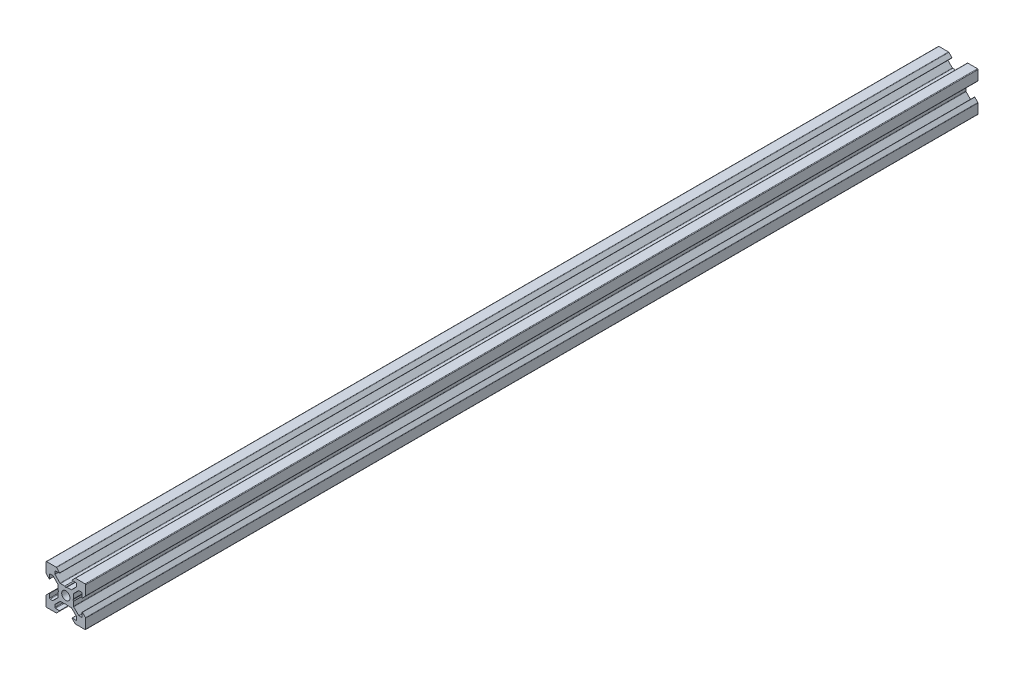
SolidWorks part; units mm, degrees
material "6063-T5"
ref_plane "Plan de face" through (0, 0, 0) normal (0, 0, 1) x (1, 0, 0)
ref_plane "Plan de dessus" through (0, 0, 0) normal (0, 1, 0) x (1, 0, 0)
ref_plane "Plan de droite" through (0, 0, 0) normal (1, 0, 0) x (0, 0, -1)
sketch "Esquisse1" plane through (0, 0, 0) normal (0, 0, 1) x (1, 0, 0)
  line L0 (18.7749, -2.8952) -> (18.7749, -4.8946)
  line L1 (18.4749, -5.1946) -> (17.2591, -5.1946)
  line L2 (17.047, -5.1067) -> (14.5634, -2.6231)
  line L3 (14.4755, -2.411) -> (14.4755, -0.2148)
  line L4 (14.4755, -0.2148) -> (14.1755, 0.3048)
  line L5 (14.1755, 0.3048) -> (14.4755, 0.8244)
  line L6 (14.4755, 0.8244) -> (14.4755, 3.0205)
  line L7 (14.5634, 3.2326) -> (17.047, 5.7162)
  line L8 (17.2591, 5.8041) -> (18.4749, 5.8041)
  line L9 (18.7749, 5.5041) -> (18.7749, 3.5048)
  line L10 (18.9456, 3.4341) -> (20.487, 4.9755)
  line L11 (20.5749, 5.1876) -> (20.5749, 10.0048)
  line L12 (20.2749, 10.3048) -> (15.4577, 10.3048)
  line L13 (15.2456, 10.2169) -> (13.7041, 8.6755)
  line L14 (13.7749, 8.5048) -> (15.7742, 8.5048)
  line L15 (16.0742, 8.2048) -> (16.0742, 6.989)
  line L16 (15.9863, 6.7769) -> (13.5027, 4.2933)
  line L17 (13.2906, 4.2054) -> (11.0945, 4.2054)
  line L18 (11.0945, 4.2054) -> (10.5749, 3.9054)
  line L19 (10.5749, 3.9054) -> (10.0552, 4.2054)
  line L20 (10.0552, 4.2054) -> (7.8591, 4.2054)
  line L21 (7.647, 4.2933) -> (5.1634, 6.7769)
  line L22 (5.0755, 6.989) -> (5.0755, 8.2048)
  line L23 (5.3755, 8.5048) -> (7.3749, 8.5048)
  line L24 (7.4456, 8.6755) -> (5.9041, 10.2169)
  line L25 (5.692, 10.3048) -> (0.8749, 10.3048)
  line L26 (0.5749, 10.0048) -> (0.5749, 5.1876)
  line L27 (0.6627, 4.9755) -> (2.2041, 3.4341)
  line L28 (2.3749, 3.5048) -> (2.3749, 5.5041)
  line L29 (2.6749, 5.8041) -> (3.8906, 5.8041)
  line L30 (4.1027, 5.7162) -> (6.5863, 3.2326)
  line L31 (6.6742, 3.0205) -> (6.6742, 0.8244)
  line L32 (6.6742, 0.8244) -> (6.9742, 0.3048)
  line L33 (6.9742, 0.3048) -> (6.6742, -0.2148)
  line L34 (6.6742, -0.2148) -> (6.6742, -2.411)
  line L35 (6.5863, -2.6231) -> (4.1027, -5.1067)
  line L36 (3.8906, -5.1946) -> (2.6749, -5.1946)
  line L37 (2.3749, -4.8946) -> (2.3749, -2.8952)
  line L38 (2.2041, -2.8245) -> (0.6627, -4.3659)
  line L39 (0.5749, -4.5781) -> (0.5749, -9.3952)
  line L40 (0.8749, -9.6952) -> (5.692, -9.6952)
  line L41 (5.9041, -9.6074) -> (7.4456, -8.0659)
  line L42 (7.3749, -7.8952) -> (5.3755, -7.8952)
  line L43 (5.0755, -7.5952) -> (5.0755, -6.3795)
  line L44 (5.1634, -6.1674) -> (7.647, -3.6838)
  line L45 (7.8591, -3.5959) -> (10.0552, -3.5959)
  line L46 (10.0552, -3.5959) -> (10.5749, -3.2959)
  line L47 (10.5749, -3.2959) -> (11.0945, -3.5959)
  line L48 (11.0945, -3.5959) -> (13.2906, -3.5959)
  line L49 (13.5027, -3.6838) -> (15.9863, -6.1674)
  line L50 (16.0742, -6.3795) -> (16.0742, -7.5952)
  line L51 (15.7742, -7.8952) -> (13.7749, -7.8952)
  line L52 (13.7041, -8.0659) -> (15.2456, -9.6074)
  line L53 (15.4577, -9.6952) -> (20.2749, -9.6952)
  line L54 (20.5749, -9.3952) -> (20.5749, -4.5781)
  line L55 (20.487, -4.3659) -> (18.9456, -2.8245)
  arc A0 (10.5749, -1.7952) -> (12.6749, 0.3048) centre (10.5749, 0.3048) ccw
  arc A1 (12.6749, 0.3048) -> (10.5749, 2.4048) centre (10.5749, 0.3048) ccw
  arc A2 (10.5749, 2.4048) -> (8.4749, 0.3048) centre (10.5749, 0.3048) ccw
  arc A3 (8.4749, 0.3048) -> (10.5749, -1.7952) centre (10.5749, 0.3048) ccw
  arc A4 (18.9456, -2.8245) -> (18.7749, -2.8952) centre (18.8749, -2.8952) ccw
  arc A5 (18.4749, -5.1946) -> (18.7749, -4.8946) centre (18.4749, -4.8946) ccw
  arc A6 (17.047, -5.1067) -> (17.2591, -5.1946) centre (17.2591, -4.8946) ccw
  arc A7 (14.4755, -2.411) -> (14.5634, -2.6231) centre (14.7755, -2.411) ccw
  arc A8 (14.5634, 3.2326) -> (14.4755, 3.0205) centre (14.7755, 3.0205) ccw
  arc A9 (17.2591, 5.8041) -> (17.047, 5.7162) centre (17.2591, 5.5041) ccw
  arc A10 (18.7749, 5.5041) -> (18.4749, 5.8041) centre (18.4749, 5.5041) ccw
  arc A11 (18.7749, 3.5048) -> (18.9456, 3.4341) centre (18.8749, 3.5048) ccw
  arc A12 (20.487, 4.9755) -> (20.5749, 5.1876) centre (20.2749, 5.1876) ccw
  arc A13 (20.5749, 10.0048) -> (20.2749, 10.3048) centre (20.2749, 10.0048) ccw
  arc A14 (15.4577, 10.3048) -> (15.2456, 10.2169) centre (15.4577, 10.0048) ccw
  arc A15 (13.7041, 8.6755) -> (13.7749, 8.5048) centre (13.7749, 8.6048) ccw
  arc A16 (16.0742, 8.2048) -> (15.7742, 8.5048) centre (15.7742, 8.2048) ccw
  arc A17 (15.9863, 6.7769) -> (16.0742, 6.989) centre (15.7742, 6.989) ccw
  arc A18 (13.2906, 4.2054) -> (13.5027, 4.2933) centre (13.2906, 4.5054) ccw
  arc A19 (7.647, 4.2933) -> (7.8591, 4.2054) centre (7.8591, 4.5054) ccw
  arc A20 (5.0755, 6.989) -> (5.1634, 6.7769) centre (5.3755, 6.989) ccw
  arc A21 (5.3755, 8.5048) -> (5.0755, 8.2048) centre (5.3755, 8.2048) ccw
  arc A22 (7.3749, 8.5048) -> (7.4456, 8.6755) centre (7.3749, 8.6048) ccw
  arc A23 (5.9041, 10.2169) -> (5.692, 10.3048) centre (5.692, 10.0048) ccw
  arc A24 (0.8749, 10.3048) -> (0.5749, 10.0048) centre (0.8749, 10.0048) ccw
  arc A25 (0.5749, 5.1876) -> (0.6627, 4.9755) centre (0.8749, 5.1876) ccw
  arc A26 (2.2041, 3.4341) -> (2.3749, 3.5048) centre (2.2749, 3.5048) ccw
  arc A27 (2.6749, 5.8041) -> (2.3749, 5.5041) centre (2.6749, 5.5041) ccw
  arc A28 (4.1027, 5.7162) -> (3.8906, 5.8041) centre (3.8906, 5.5041) ccw
  arc A29 (6.6742, 3.0205) -> (6.5863, 3.2326) centre (6.3742, 3.0205) ccw
  arc A30 (6.5863, -2.6231) -> (6.6742, -2.411) centre (6.3742, -2.411) ccw
  arc A31 (3.8906, -5.1946) -> (4.1027, -5.1067) centre (3.8906, -4.8946) ccw
  arc A32 (2.3749, -4.8946) -> (2.6749, -5.1946) centre (2.6749, -4.8946) ccw
  arc A33 (2.3749, -2.8952) -> (2.2041, -2.8245) centre (2.2749, -2.8952) ccw
  arc A34 (0.6627, -4.3659) -> (0.5749, -4.5781) centre (0.8749, -4.5781) ccw
  arc A35 (0.5749, -9.3952) -> (0.8749, -9.6952) centre (0.8749, -9.3952) ccw
  arc A36 (5.692, -9.6952) -> (5.9041, -9.6074) centre (5.692, -9.3952) ccw
  arc A37 (7.4456, -8.0659) -> (7.3749, -7.8952) centre (7.3749, -7.9952) ccw
  arc A38 (5.0755, -7.5952) -> (5.3755, -7.8952) centre (5.3755, -7.5952) ccw
  arc A39 (5.1634, -6.1674) -> (5.0755, -6.3795) centre (5.3755, -6.3795) ccw
  arc A40 (7.8591, -3.5959) -> (7.647, -3.6838) centre (7.8591, -3.8959) ccw
  arc A41 (13.5027, -3.6838) -> (13.2906, -3.5959) centre (13.2906, -3.8959) ccw
  arc A42 (16.0742, -6.3795) -> (15.9863, -6.1674) centre (15.7742, -6.3795) ccw
  arc A43 (15.7742, -7.8952) -> (16.0742, -7.5952) centre (15.7742, -7.5952) ccw
  arc A44 (13.7749, -7.8952) -> (13.7041, -8.0659) centre (13.7749, -7.9952) ccw
  arc A45 (15.2456, -9.6074) -> (15.4577, -9.6952) centre (15.4577, -9.3952) ccw
  arc A46 (20.2749, -9.6952) -> (20.5749, -9.3952) centre (20.2749, -9.3952) ccw
  arc A47 (20.5749, -4.5781) -> (20.487, -4.3659) centre (20.2749, -4.5781) ccw
extrude "Boss.-Extru.1" add sketch "Esquisse1" along normal blind 450
